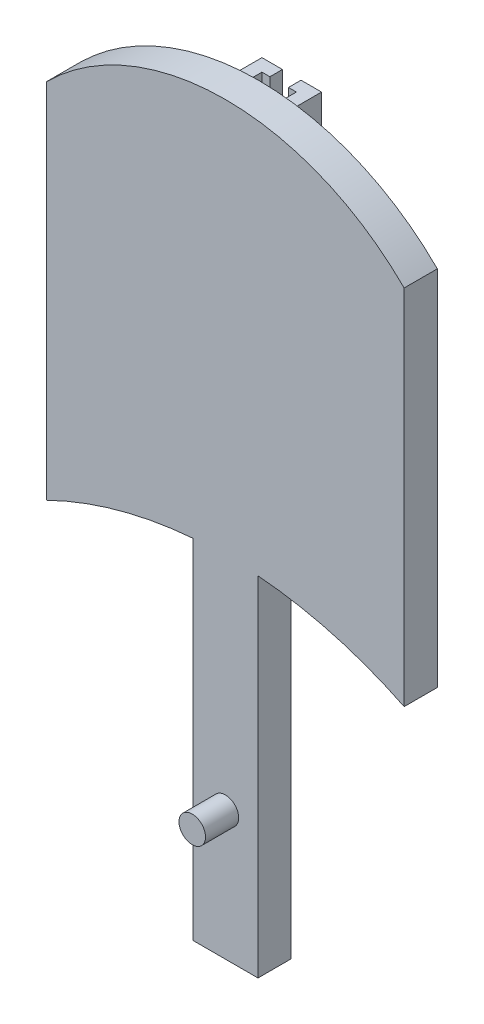
SolidWorks part; units mm, degrees
ref_plane "Front Plane" through (0, 0, 0) normal (0, 0, 1) x (1, 0, 0)
ref_plane "Top Plane" through (0, 0, 0) normal (0, 1, 0) x (1, 0, 0)
ref_plane "Right Plane" through (0, 0, 0) normal (1, 0, 0) x (0, 0, -1)
sketch "Sketch1" plane through (0, 0, 0) normal (0, 0, 1) x (1, 0, 0)
  line L1 (-17.1143, -17.3576) -> (17.1143, -17.3576)
  line L2 (-17.1143, -17.3576) -> (-17.1143, 17.3576)
  line L3 (-17.1143, 17.3576) -> (17.1143, 17.3576)
  line L4 (17.1143, -17.3576) -> (17.1143, 17.3576)
  line L5 (-17.1143, -17.3576) -> (17.1143, 17.3576) construction
  line L6 (-17.1143, 17.3576) -> (17.1143, -17.3576) construction
  arc A2 (-17.1143, 17.3576) -> (17.1143, 17.3576) centre (0, 0.1943) cw
  arc A3 (-17.1143, -17.3576) -> (17.1143, -17.3576) centre (0, -52.2147) cw
  point P0 (0, 0)
extrude "Boss-Extrude1" add sketch "Sketch1" along normal blind 3.175 contours A2 L3 | L2 A3 L4 L3
sketch "Sketch2" plane through (0, 0, 0) normal (0, 0, -1) x (-1, 0, 0)
  line L0 (1.6513, 22.2683) -> (1.6513, 23.2984)
  line L1 (-1.6513, -22.2683) -> (1.6513, -22.2683)
  line L2 (-1.6513, -22.2683) -> (-1.6513, 22.2683)
  line L3 (-1.6513, 22.2683) -> (1.6513, 22.2683)
  line L4 (1.6513, -22.2683) -> (1.6513, 22.2683)
  line L5 (-1.6513, -22.2683) -> (1.6513, 22.2683) construction
  line L6 (-1.6513, 22.2683) -> (1.6513, -22.2683) construction
  line L7 (-2.8534, -23.2984) -> (2.8534, -23.2984)
  line L8 (-2.8534, -23.2984) -> (-2.8534, 23.2984)
  line L9 (-2.8534, 23.2984) -> (2.8534, 23.2984)
  line L10 (2.8534, -23.2984) -> (2.8534, 23.2984)
  line L11 (-2.8534, -23.2984) -> (2.8534, 23.2984) construction
  line L12 (-2.8534, 23.2984) -> (2.8534, -23.2984) construction
  line L13 (-1.6513, 22.2683) -> (-1.6513, 23.2984)
  arc A0 (17.1143, -17.3576) -> (-17.1143, -17.3576) centre (0, -52.2147) ccw construction
  arc A1 (17.1143, -17.3576) -> (-17.1143, -17.3576) centre (0, -52.2147) ccw
  point P0 (0, 0)
  point P5 (0, 0)
  arc M3 (-17.1143, -17.3576) -> (17.1143, -17.3576) centre (0, -52.2147) cw
  dimension "D1" = 1.2021
  dimension "D2" = 3.3026
extrude "Boss-Extrude2" add sketch "Sketch2" along normal blind 3.175 contours L2 L13 L9 L8 M3 | L10 L9 L0 L4 M3
sketch "Sketch3" plane through (0, 0, 3.175) normal (0, 0, 1) x (1, 0, 0)
  line L0 (-3.1185, 0.3389) -> (3.1185, 0.3389)
  line L2 (-3.1185, 0.3389) -> (-3.1185, -46.8558)
  line L3 (-3.1185, -46.8558) -> (3.1185, -46.8558)
  line L4 (3.1185, 0.3389) -> (3.1185, -46.8558)
  line L5 (-0.0226, 0.3389) -> (3.1185, -46.8558) construction
  line L6 (-3.1185, -46.8558) -> (0.0226, 0.3389) construction
  point P0 (0, 0)
extrude "Boss-Extrude3" add sketch "Sketch3" against normal blind 3.175
sketch "Sketch4" plane through (0, 0, 3.175) normal (0, 0, 1) x (1, 0, 0)
  line L0 (0, -46.8558) -> (0, -34.5037)
  line L1 (-3.1185, -46.8558) -> (3.1185, -46.8558) construction
  circle A0 centre (0, -34.5037) radius 1.27
  dimension "D1" = 2.54
extrude "Boss-Extrude4" add sketch "Sketch4" along normal blind 3.175
sketch "Sketch5" plane through (0, 0, 6.35) normal (0, 0, 1) x (1, 0, 0)
  point P0 (0, -34.5037)
sketch "Sketch6" plane through (1.6513, 0, 0) normal (-1, 0, 0) x (0, 0, 1)
  line L0 (-3.175, 23.2984) -> (-1.9729, 23.2984)
  line L1 (-3.175, 23.2984) -> (0, 23.2984) construction
  line L2 (-1.9729, 23.2984) -> (-1.9729, -13.4179)
  line L3 (-3.175, -13.4179) -> (0, -13.4179) construction
  line L4 (-1.9729, -13.4179) -> (-3.175, -13.4179)
  line L5 (-3.175, -13.4179) -> (-3.175, 23.2984)
  dimension "D1" = 1.2021
extrude "Boss-Extrude5" add sketch "Sketch6" along normal up to next
sketch "Sketch8" plane through (0, 0, -3.175) normal (0, 0, -1) x (-1, 0, 0)
  line L0 (0, 23.2984) -> (-0.889, 23.2984)
  line L1 (-2.8534, 23.2984) -> (2.8534, 23.2984) construction
  line L2 (0, 23.2984) -> (0.889, 23.2984)
  line L3 (0.889, 23.2984) -> (0.889, -13.4179)
  line L4 (1.6513, -13.4179) -> (-1.6513, -13.4179) construction
  line L5 (0.889, -13.4179) -> (-0.889, -13.4179)
  line L6 (-0.889, -13.4179) -> (-0.889, 23.2984)
  dimension "D1" = 1.778
  dimension "D2" = 0.889
extrude "Cut-Extrude1" cut sketch "Sketch8" against normal up to next
